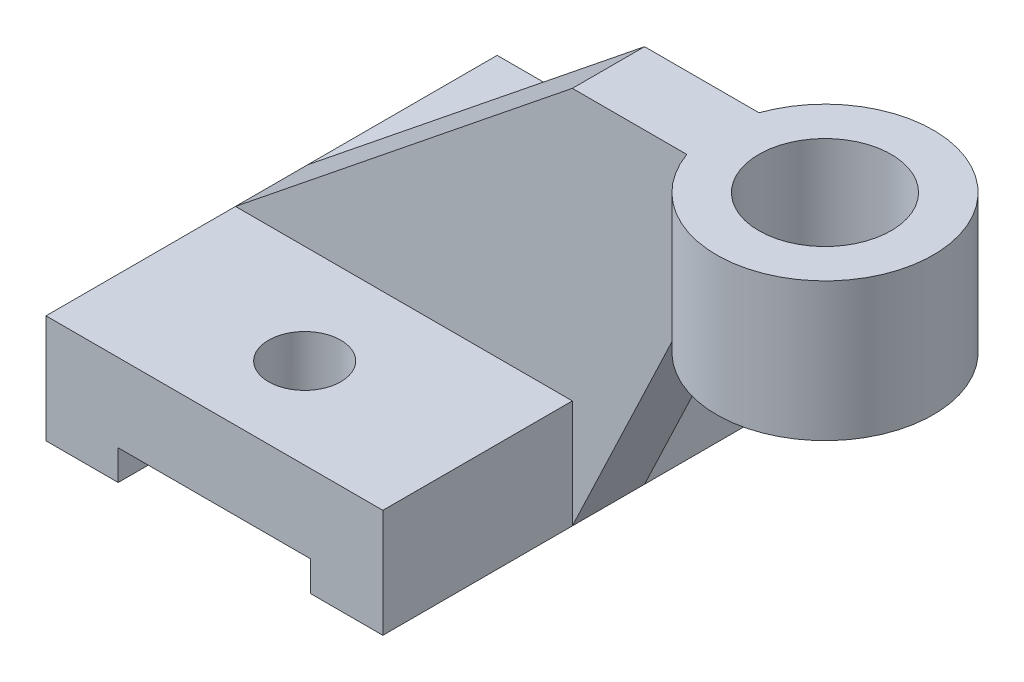
SolidWorks part; units mm, degrees
ref_plane "Ön Düzlem" through (0, 0, 0) normal (0, 0, 1) x (1, 0, 0)
ref_plane "Üst Düzlem" through (0, 0, 0) normal (0, 1, 0) x (1, 0, 0)
ref_plane "Sağ Düzlem" through (0, 0, 0) normal (1, 0, 0) x (0, 0, -1)
sketch "Çizim1" plane through (0, 0, 0) normal (0, 1, 0) x (1, 0, 0)
  line L1 (0, 0) -> (56, 0)
  line L2 (0, 0) -> (0, -75)
  line L3 (0, -75) -> (56, -75)
  line L4 (56, 0) -> (56, -75)
  dimension "D1" = 75
  dimension "D2" = 56
extrude "Yükseklik-Ekstrüzyon1" add sketch "Çizim1" along normal blind 18 contours L2 L3 L4 L1
sketch "Çizim3" plane through (0, 18, 0) normal (0, 1, 0) x (1, 0, 0)
  line L0 (0, 0) -> (28, 0)
  line L1 (0, 0) -> (56, 0) construction
  line L2 (28, 0) -> (28, -15)
  line L3 (0, -37.5) -> (56, -37.5) construction
  line L4 (0, 0) -> (0, -75) construction
  line L5 (56, 0) -> (56, -75) construction
  circle A0 centre (28, -15) radius 6
  circle A1 centre (28, -60) radius 6
  dimension "D3" = 12
  dimension "D1" = 28
  dimension "D2" = 15
extrude "Kes-Ekstrüzyon1" cut sketch "Çizim3" against normal through all
sketch "Çizim4" plane through (0, 0, 75) normal (0, 0, 1) x (1, 0, 0)
  line L0 (56, 0) -> (44, 0)
  line L1 (0, 0) -> (56, 0) construction
  line L2 (44, 0) -> (12, 0)
  line L3 (12, 0) -> (12, 5)
  line L4 (12, 5) -> (44, 5)
  line L5 (44, 5) -> (44, 0)
  line M1 (0, 0) -> (56, 0)
  dimension "D1" = 12
  dimension "D2" = 32
  dimension "D3" = 5
extrude "Kes-Ekstrüzyon2" cut sketch "Çizim4" against normal through all contours L5 L4 L3 M1
ref_plane "Düzlem1" through (0, 0, 37.5) normal (0, 0, 1) x (1, 0, 0)
sketch "Çizim5" plane through (0, 0, 37.5) normal (0, 0, 1) x (1, 0, 0)
  line L0 (0, 18) -> (56, 18)
  line L1 (56, 18) -> (56, 63)
  line L2 (0, 18) -> (56, 63)
  dimension "D1" = 45
extrude "Yükseklik-Ekstrüzyon2" add sketch "Çizim5" along normal mid plane 12
ref_plane "Düzlem2" through (0, 63, 0) normal (0, 1, 0) x (1, 0, 0)
sketch "Çizim7" plane through (0, 63, 0) normal (0, 1, 0) x (1, 0, 0)
  line L0 (56, -31.5) -> (75.0294, -31.5)
  line L1 (56, -43.5) -> (75.0294, -43.5)
  line L2 (56, -37.5) -> (92, -37.5) construction
  line L3 (56, -43.5) -> (56, -31.5) construction
  line L4 (56, -31.5) -> (56, -37.5)
  line L5 (56, -37.5) -> (56, -43.5)
  circle A0 centre (92, -37.5) radius 11
  arc A1 (75.0294, -43.5) -> (75.0294, -31.5) centre (92, -37.5) ccw
  point P1 (75.0294, -43.5)
  dimension "D3" = 22
  dimension "D4" = 36
  dimension "D1" = 36
extrude "Yükseklik-Ekstrüzyon3" add sketch "Çizim7" against normal blind 23
sketch "Çizim8" plane through (0, 0, 37.5) normal (0, 0, 1) x (1, 0, 0)
  line L0 (56, 0) -> (75.0294, 40)
rib "Feder1" sketch "Çizim8" sketch "Çizim8" thickness 12 extrusion direction parallel to sketch draft on no parameters "D1"=12
